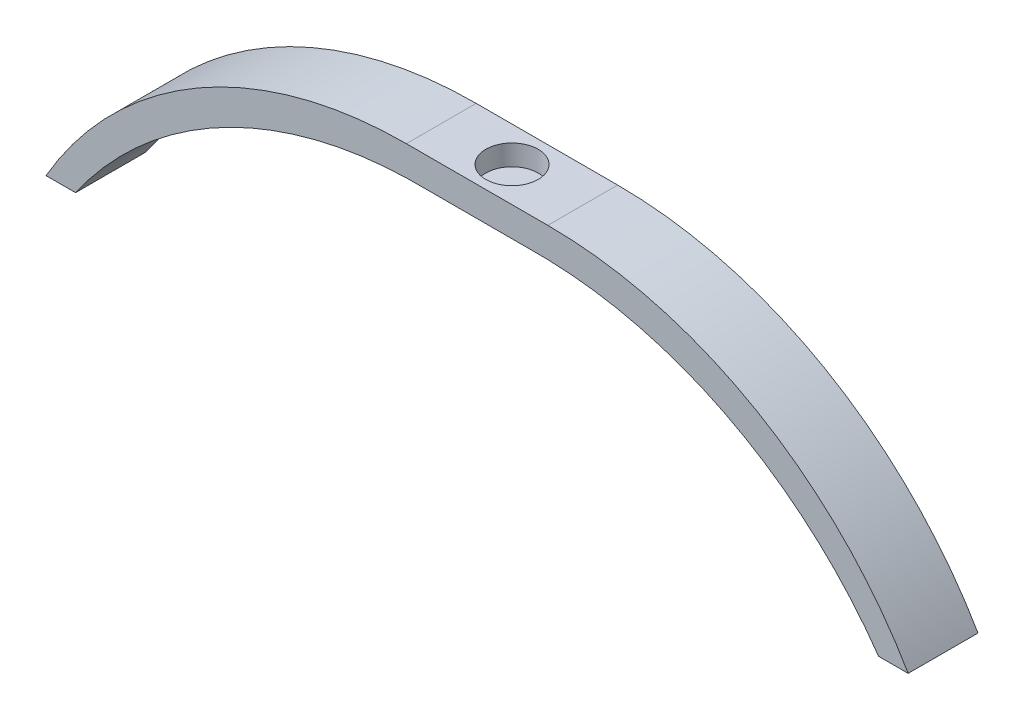
SolidWorks part; units mm, degrees
ref_plane "Front Plane" through (0, 0, 0) normal (0, 0, 1) x (1, 0, 0)
ref_plane "Top Plane" through (0, 0, 0) normal (0, 1, 0) x (1, 0, 0)
ref_plane "Right Plane" through (0, 0, 0) normal (1, 0, 0) x (0, 0, -1)
sketch "Sketch1" plane through (0, 0, 0) normal (0, 1, 0) x (1, 0, 0)
  line L1 (-7.62, 5.08) -> (7.62, 5.08)
  line L2 (-7.62, 5.08) -> (-7.62, -5.08)
  line L3 (-7.62, -5.08) -> (7.62, -5.08)
  line L4 (7.62, 5.08) -> (7.62, -5.08)
  line L5 (-7.62, 5.08) -> (7.62, -5.08) construction
  line L6 (-7.62, -5.08) -> (7.62, 5.08) construction
  point P0 (0, 0)
  dimension "D1" = 15.24
  dimension "D2" = 10.16
extrude "Boss-Extrude1" add sketch "Sketch1" along normal blind 4.3
sketch "Sketch2" plane through (0, 0, 5.08) normal (0, 0, 1) x (1, 0, 0)
  line L2 (0, 8.529) -> (0, -7.8099) construction
  line L7 (7.62, 0) -> (10.29, -0.0202)
  line L8 (7.62, 4.3) -> (10.29, 4.3)
  line L9 (-7.62, 4.3) -> (7.62, 4.3) construction
  line L10 (0, 4.3) -> (62.7192, 4.3) construction
  line L13 (62.7192, -25.94) -> (58.4192, -25.94)
  line L14 (0, 4.3) -> (10.29, 4.3)
  line L15 (62.7192, 4.3) -> (62.7192, -25.94) construction
  line L16 (7.62, 4.3) -> (7.62, 0)
  line L24 (-62.7192, -25.94) -> (-58.4192, -25.94)
  line L25 (-7.62, 0) -> (-10.29, -0.0202)
  line L26 (-7.62, 4.3) -> (-7.62, 0)
  line L27 (-7.62, 4.3) -> (-10.29, 4.3)
  arc A4 (10.29, -0.0202) -> (58.4192, -25.94) centre (8.7252, -60.57) cw
  arc A7 (62.7192, -25.94) -> (10.29, 4.3) centre (10.29, -56.27) ccw
  arc A8 (-62.7192, -25.94) -> (-10.29, 4.3) centre (-10.29, -56.27) cw
  arc A9 (-10.29, -0.0202) -> (-58.4192, -25.94) centre (-8.7252, -60.57) ccw
  dimension "D2" = 4.3
  dimension "D5" = 121.14
  dimension "D3" = 60.57
  dimension "D4" = 2.67
extrude "Boss-Extrude2" add sketch "Sketch2" against normal up to surface (10.16 mm away) up to face at (0, 2.15, -5.08)
sketch "Sketch3" plane through (0, 4.3, 0) normal (0, 1, 0) x (1, 0, 0)
  circle A0 centre (0, 0) radius 3.81
  dimension "D1" = 7.62
extrude "Cut-Extrude1" cut sketch "Sketch3" against normal blind 3
